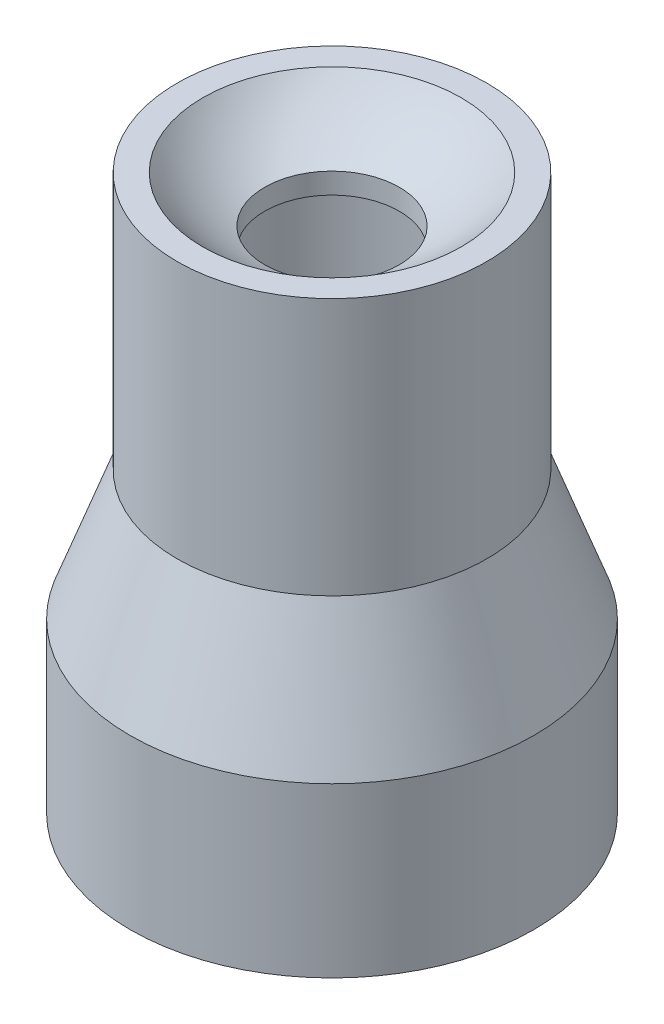
SolidWorks part; units mm, degrees
ref_plane "Front Plane" through (0, 0, 0) normal (0, 0, 1) x (1, 0, 0)
ref_plane "Top Plane" through (0, 0, 0) normal (0, 1, 0) x (1, 0, 0)
ref_plane "Right Plane" through (0, 0, 0) normal (1, 0, 0) x (0, 0, -1)
sketch "Sketch1" plane through (0, 0, 0) normal (0, 0, 1) x (1, 0, 0)
  line L0 (6, 0) -> (5, 0)
  line L1 (4.6, 16.5) -> (4.6, 8.8465)
  line L2 (4.6, 16.5) -> (3.8419, 16.5)
  line L3 (0, 14.8) -> (0, 14.6) construction
  line L4 (5, 0) -> (5, 5)
  line L5 (6, 0) -> (6, 5)
  line L6 (5, 5) -> (3.6, 5)
  line L7 (2, 14.5) -> (2, 15.1174)
  line L9 (3.6, 5) -> (3.6, 14.5)
  line L10 (3.6, 14.5) -> (2, 14.5)
  line L11 (6, 5) -> (4.6, 8.8465)
  arc A0 (2, 15.1174) -> (3.8419, 16.5) centre (0, 19.7) ccw
  dimension "D8" = 10
  dimension "D9" = 5.2
  dimension "D1" = 5
  dimension "D2" = 1
  dimension "D3" = 1
  dimension "D4" = 3.6
  dimension "D5" = 5
  dimension "D6" = 20
  dimension "D7" = 9.5
  dimension "D10" = 2
  dimension "D11" = 2
revolve "Revolve1" add sketch "Sketch1" angle 360 about L3
